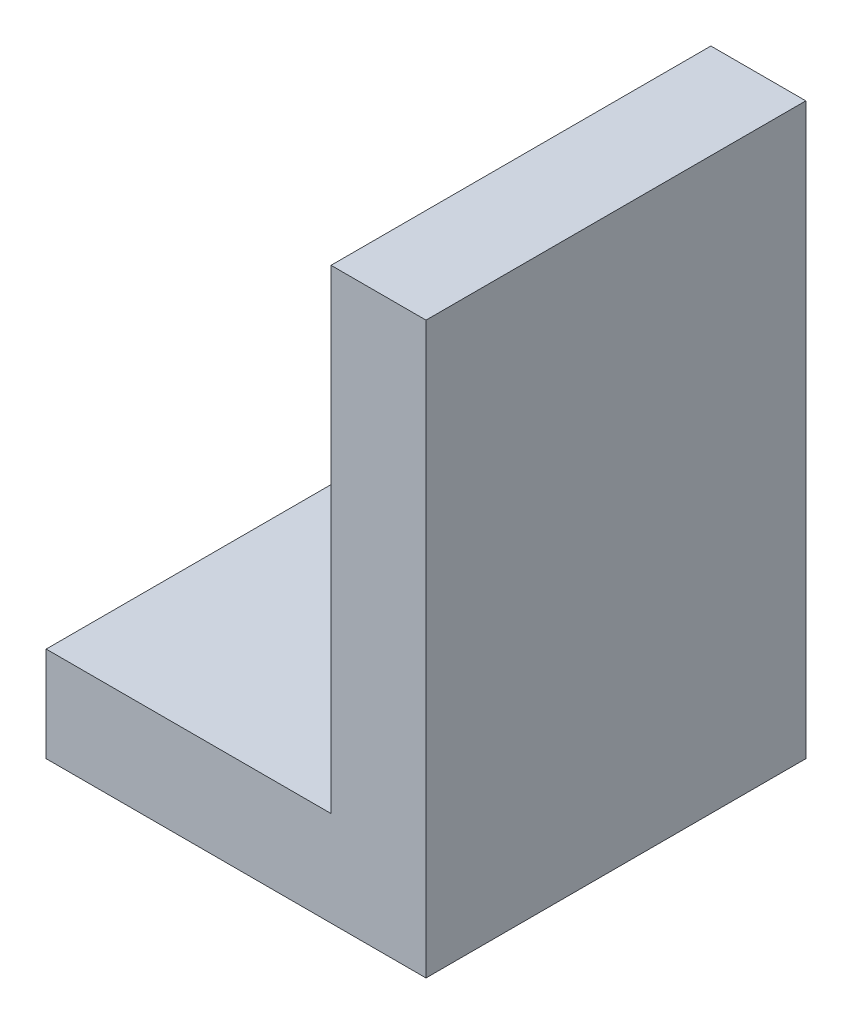
SolidWorks part; units mm, degrees
ref_plane "Front Plane" through (0, 0, 0) normal (0, 0, 1) x (1, 0, 0)
ref_plane "Top Plane" through (0, 0, 0) normal (0, 1, 0) x (1, 0, 0)
ref_plane "Right Plane" through (0, 0, 0) normal (1, 0, 0) x (0, 0, -1)
sketch "Sketch1" plane through (0, 0, 0) normal (0, 1, 0) x (1, 0, 0)
  line L1 (8.3544, 5.7215) -> (-31.6456, 5.7215)
  line L2 (8.3544, 5.7215) -> (8.3544, -34.2785)
  line L3 (8.3544, -34.2785) -> (-31.6456, -34.2785)
  line L4 (-31.6456, 5.7215) -> (-31.6456, -34.2785)
  dimension "D1" = 40
  dimension "D2" = 40
extrude "Boss-Extrude1" add sketch "Sketch1" along normal blind 10
sketch "Sketch2" plane through (0, 10, 0) normal (0, 1, 0) x (1, 0, 0)
  line L0 (-31.6456, -34.2785) -> (8.3544, -34.2785) construction
  line L1 (8.3544, 5.7215) -> (-1.6456, 5.7215)
  line L2 (8.3544, 5.7215) -> (8.3544, -34.2785)
  line L3 (8.3544, -34.2785) -> (-1.6456, -34.2785)
  line L4 (-1.6456, 5.7215) -> (-1.6456, -34.2785)
  dimension "D1" = 10
extrude "Boss-Extrude2" add sketch "Sketch2" along normal blind 50
